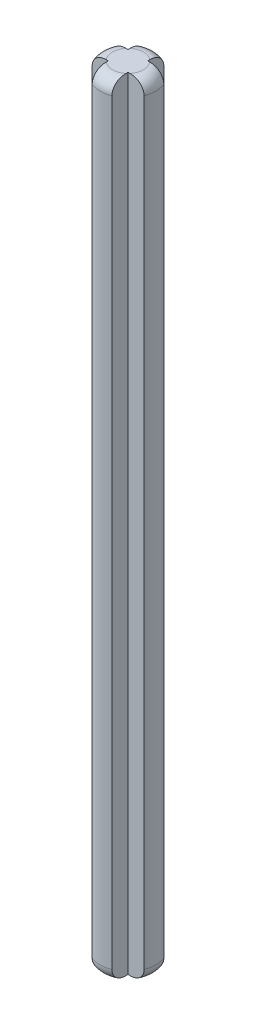
SolidWorks part; units mm, degrees
ref_plane "Front Plane" through (0, 0, 0) normal (0, 0, 1) x (1, 0, 0)
ref_plane "Top Plane" through (0, 0, 0) normal (0, 1, 0) x (1, 0, 0)
ref_plane "Right Plane" through (0, 0, 0) normal (1, 0, 0) x (0, 0, -1)
sketch "Sketch1" plane through (0, 0, 0) normal (0, 1, 0) x (1, 0, 0)
  line L0 (-0.8, -0.8) -> (-0.8, -2.103)
  line L1 (-0.8, 0.8) -> (-2.103, 0.8)
  line L2 (2.103, 0.8) -> (0.8, 0.8)
  line L3 (2.103, -0.8) -> (0.8, -0.8)
  line L4 (0.8, -0.8) -> (0.8, -2.103)
  line L5 (-0.8, -0.8) -> (-2.103, -0.8)
  line L6 (-7.75, 0) -> (-7.75, 0)
  line L7 (-7.75, 0) -> (-7.75, 0)
  line L8 (-0.8, 2.103) -> (-0.8, 0.8)
  line L9 (0.8, 2.103) -> (0.8, 0.8)
  line L10 (-7.75, 0) -> (-7.75, 0)
  line L11 (7.75, 0) -> (7.75, 0)
  line L12 (7.75, 0) -> (7.75, 0)
  line L13 (7.75, 0) -> (7.75, 0)
  line L14 (7.75, 0) -> (7.75, 0)
  line L15 (-7.75, 0) -> (-7.75, 0)
  line L16 (-8.6621, 8.6621) -> (-8.6621, 8.6621)
  line L17 (-8.6621, -8.6621) -> (-8.6621, -8.6621)
  line L18 (-8.6621, -8.6621) -> (-8.6621, -8.6621)
  line L19 (8.6621, -8.6621) -> (8.6621, -8.6621)
  line L20 (8.6621, -8.6621) -> (8.6621, -8.6621)
  line L21 (8.6621, 8.6621) -> (8.6621, 8.6621)
  line L22 (8.6621, 8.6621) -> (8.6621, 8.6621)
  line L23 (-8.6621, 8.6621) -> (-8.6621, 8.6621)
  arc A0 (-2.103, 0.8) -> (-2.103, -0.8) centre (0, 0) ccw
  arc A1 (0.8, 2.103) -> (-0.8, 2.103) centre (0, 0) ccw
  arc A2 (2.103, -0.8) -> (2.103, 0.8) centre (0, 0) ccw
  arc A3 (-0.8, -2.103) -> (0.8, -2.103) centre (0, 0) ccw
  arc A4 (-7.75, 0) -> (-7.75, 0) centre (-7.75, 0) ccw
  arc A5 (-7.75, 0) -> (7.75, 0) centre (0, 0) ccw
  arc A6 (7.75, 0) -> (7.75, 0) centre (7.75, 0) ccw
  arc A7 (7.75, 0) -> (-7.75, 0) centre (0, 0) ccw
  arc A8 (-8.6621, 8.6621) -> (-8.6621, -8.6621) centre (0, 0) ccw
  arc A9 (-8.6621, -8.6621) -> (8.6621, -8.6621) centre (0, 0) ccw
  arc A10 (8.6621, -8.6621) -> (8.6621, 8.6621) centre (0, 0) ccw
  arc A11 (8.6621, 8.6621) -> (-8.6621, 8.6621) centre (0, 0) ccw
  point P26 (0.8, 0)
  dimension "D1" = 4.5
  dimension "D2" = 10
  dimension "D3" = 10
extrude "Boss-Extrude1" add sketch "Sketch1" along normal offset from surface (63.3 mm away) 63.3 contours L0 A3 L4 L3 A2 L2 L9 A1 L8 L1 A0 L5 up to plane "Top Plane"
fillet "Fillet1" radius 1 1 edges at (-2.25, 0, 0)
fillet "Fillet2" radius 1 1 edges at (0, 0, 2.25)
fillet "Fillet3" radius 1 1 edges at (2.25, 0, 0)
fillet "Fillet4" radius 1 1 edges at (0, 0, -2.25)
fillet "Fillet20" radius 1 1 edges at (2.25, 63.3, 0)
fillet "Fillet21" radius 1 1 edges at (0, 63.3, 2.25)
fillet "Fillet22" radius 1 1 edges at (-2.25, 63.3, 0)
fillet "Fillet23" radius 1 1 edges at (0, 63.3, -2.25)
